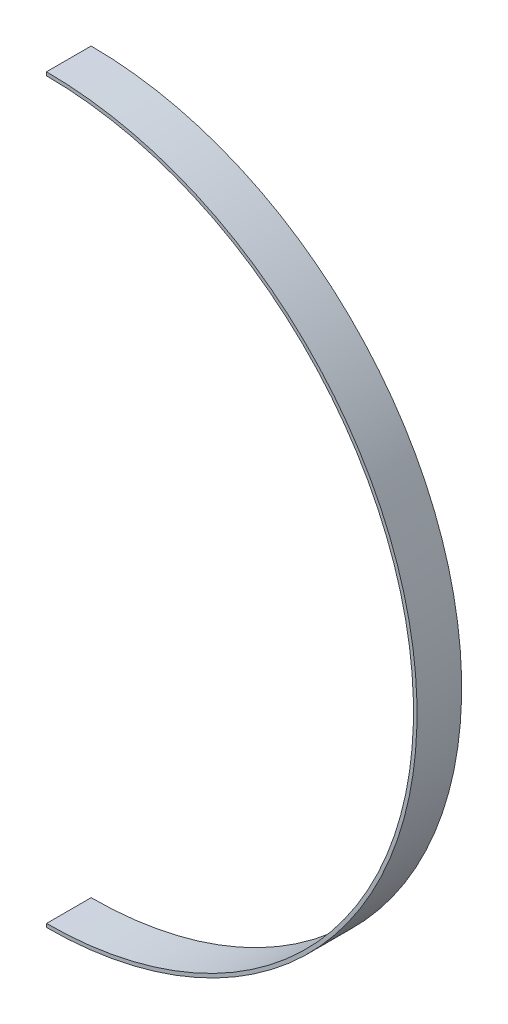
SolidWorks part; units mm, degrees
material "EPDM 60 Durometer"
ref_plane "Front" through (0, 0, 0) normal (0, 0, 1) x (1, 0, 0)
ref_plane "Top" through (0, 0, 0) normal (0, 1, 0) x (1, 0, 0)
ref_plane "Right" through (0, 0, 0) normal (1, 0, 0) x (0, 0, -1)
sketch "Sketch1" plane through (0, 0, 0) normal (0, 0, 1) x (1, 0, 0)
  line L0 (0, 83.05) -> (0, 82.2563)
  line L1 (0, -82.2563) -> (0, -83.05)
  arc A0 (0, -82.2563) -> (0, 82.2563) centre (0, 0) ccw
  arc A1 (0, -83.05) -> (0, 83.05) centre (0, 0) ccw
  circle A2 centre (0, 0) radius 83.05 construction
  circle A3 centre (0, 0) radius 82.2563 construction
  dimension "D1" = 83.05
  dimension "D2" = 0.7937
extrude "Boss-Extrude1" add sketch "Sketch1" along normal blind 10 contours A1 L0 A0 L1
